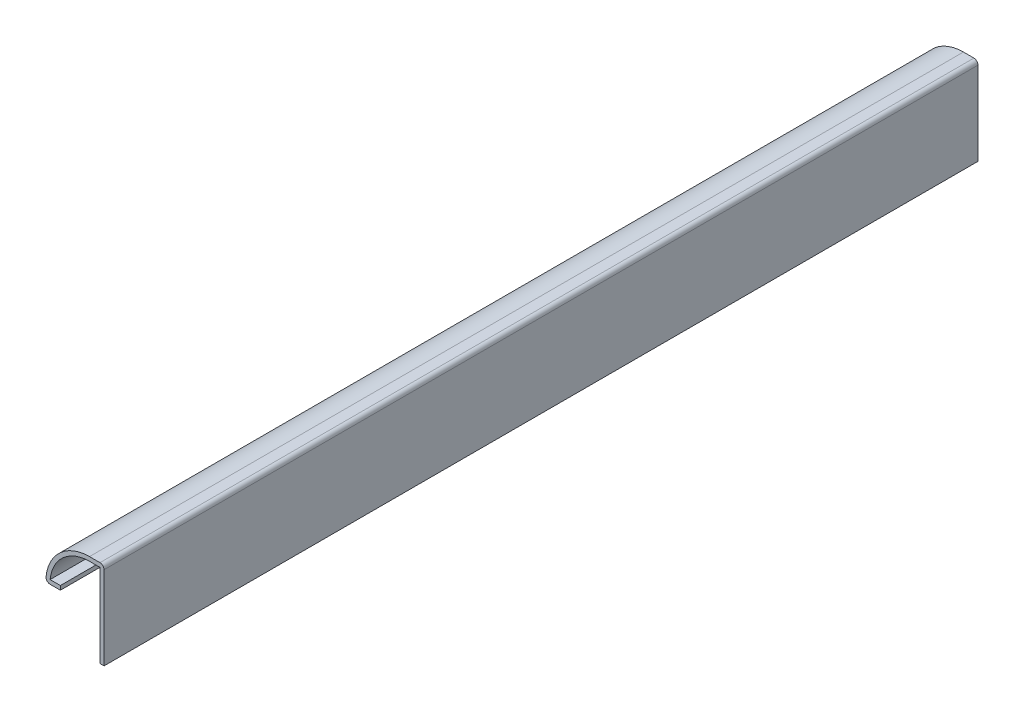
SolidWorks part; units mm, degrees
ref_plane "Front Plane" through (0, 0, 0) normal (0, 0, 1) x (1, 0, 0)
ref_plane "Top Plane" through (0, 0, 0) normal (0, 1, 0) x (1, 0, 0)
ref_plane "Right Plane" through (0, 0, 0) normal (1, 0, 0) x (0, 0, -1)
sketch "Sketch1" plane through (0, 0, 0) normal (0, 0, 1) x (1, 0, 0)
  line L0 (0, 0) -> (0, 19.05)
  line L1 (0, 19.05) -> (-3.175, 19.05)
  line L2 (-12.7, 9.525) -> (-9.525, 9.525)
  arc A0 (-3.175, 19.05) -> (-12.7, 9.525) centre (-3.175, 9.525) ccw
  point P6 (-3.8505, 10.2005)
  dimension "D1" = 19.05
  dimension "D2" = 12.7
  dimension "D3" = 9.525
  dimension "D4" = 3.175
extrude "Extrude-Thin1" add sketch "Sketch1" against normal blind 190.5 thin thin type one direction reverse wall 0.889
fillet "Fillet1" radius 0.889 2 edges at (0, 19.05, -95.25) (-12.7, 9.525, -95.25)
